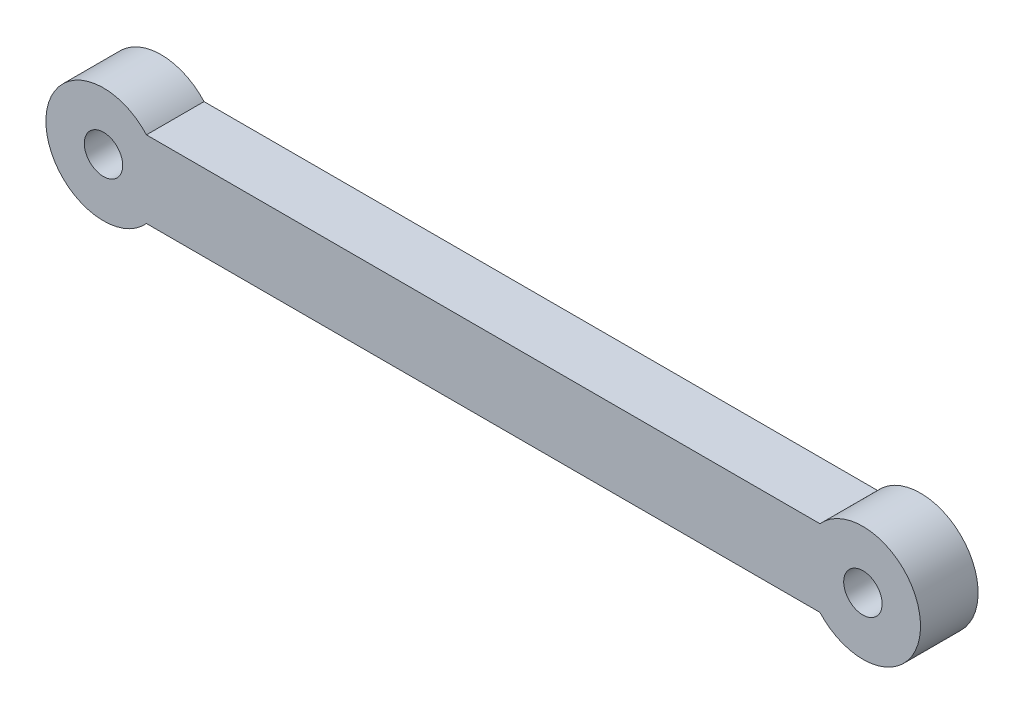
SolidWorks part; units mm, degrees
material "Acrylic (Medium-high impact)"
ref_plane "Front Plane" through (0, 0, 0) normal (0, 0, 1) x (1, 0, 0)
ref_plane "Top Plane" through (0, 0, 0) normal (0, 1, 0) x (1, 0, 0)
ref_plane "Right Plane" through (0, 0, 0) normal (1, 0, 0) x (0, 0, -1)
sketch "Sketch1" plane through (0, 0, 0) normal (0, 0, 1) x (1, 0, 0)
  line L3 (-41.4027, 25.83) -> (-6.3248, 25.83)
  line L6 (-41.4027, 21.83) -> (-6.3248, 21.83)
  line L7 (-6.3248, 25.83) -> (-6.3248, 21.83) construction
  line L9 (-41.4027, 25.83) -> (-41.4027, 21.83) construction
  circle A2 centre (-4.0887, 23.83) radius 1
  circle A13 centre (-43.6387, 23.83) radius 1
  arc A14 (-41.4027, 25.83) -> (-41.4027, 21.83) centre (-43.6387, 23.83) ccw
  arc A16 (-6.3248, 25.83) -> (-6.3248, 21.83) centre (-4.0887, 23.83) cw
  dimension "D3" = 2
  dimension "D4" = 2
  dimension "D7" = 39.55
  dimension "D1" = 2
  dimension "D2" = 4
  dimension "D6" = 2
extrude "Boss-Extrude1" add sketch "Sketch1" along normal blind 3
